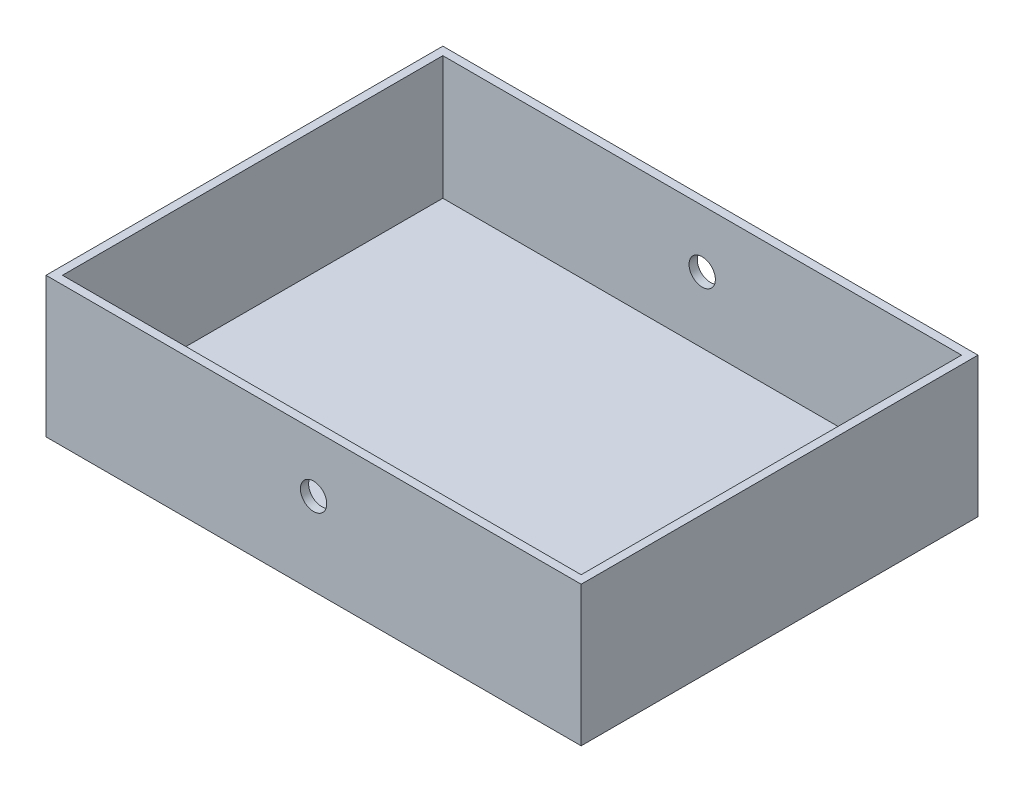
SolidWorks part; units mm, degrees
material "201 Annealed Stainless Steel (SS)"
ref_plane "Front Plane" through (0, 0, 0) normal (0, 0, 1) x (1, 0, 0)
ref_plane "Top Plane" through (0, 0, 0) normal (0, 1, 0) x (1, 0, 0)
ref_plane "Right Plane" through (0, 0, 0) normal (1, 0, 0) x (0, 0, -1)
sketch "Sketch1" plane through (0, 0, 0) normal (0, 0, 1) x (1, 0, 0)
  line L1 (325, -85) -> (-325, -85)
  line L2 (325, -85) -> (325, 85)
  line L3 (325, 85) -> (-325, 85)
  line L4 (-325, -85) -> (-325, 85)
  line L5 (325, -85) -> (-325, 85) construction
  line L6 (325, 85) -> (-325, -85) construction
  point P0 (0, 0)
  dimension "D1" = 650
  dimension "D2" = 170
extrude "Boss-Extrude1" add sketch "Sketch1" along normal blind 482
sketch "Sketch2" plane through (0, 0, 0) normal (0, 0, -1) x (-1, 0, 0)
  line L1 (325, -85) -> (-325, -85) construction
  circle A0 centre (0, 15) radius 16
  dimension "D2" = 32
  dimension "D1" = 100
extrude "Cut-Extrude1" cut sketch "Sketch2" against normal through all
sketch "Sketch3" plane through (0, 85, 0) normal (0, 1, 0) x (1, 0, 0)
  line L0 (-325, -241) -> (325, -241) construction
  line L1 (-325, -482) -> (-325, 0) construction
  line L2 (325, -482) -> (325, 0) construction
  line L3 (0, 0) -> (0, -482) construction
  line L4 (325, -482) -> (-325, -482) construction
  line L5 (325, 0) -> (-325, 0) construction
  line L6 (-315, -472) -> (315, -472)
  line L7 (-315, -472) -> (-315, -10)
  line L8 (-315, -10) -> (315, -10)
  line L9 (315, -472) -> (315, -10)
  line L10 (-315, -472) -> (315, -10) construction
  line L11 (-315, -10) -> (315, -472) construction
  point P11 (0, -241)
  dimension "D1" = 10
  dimension "D2" = 10
extrude "Cut-Extrude2" cut sketch "Sketch3" against normal blind 150
